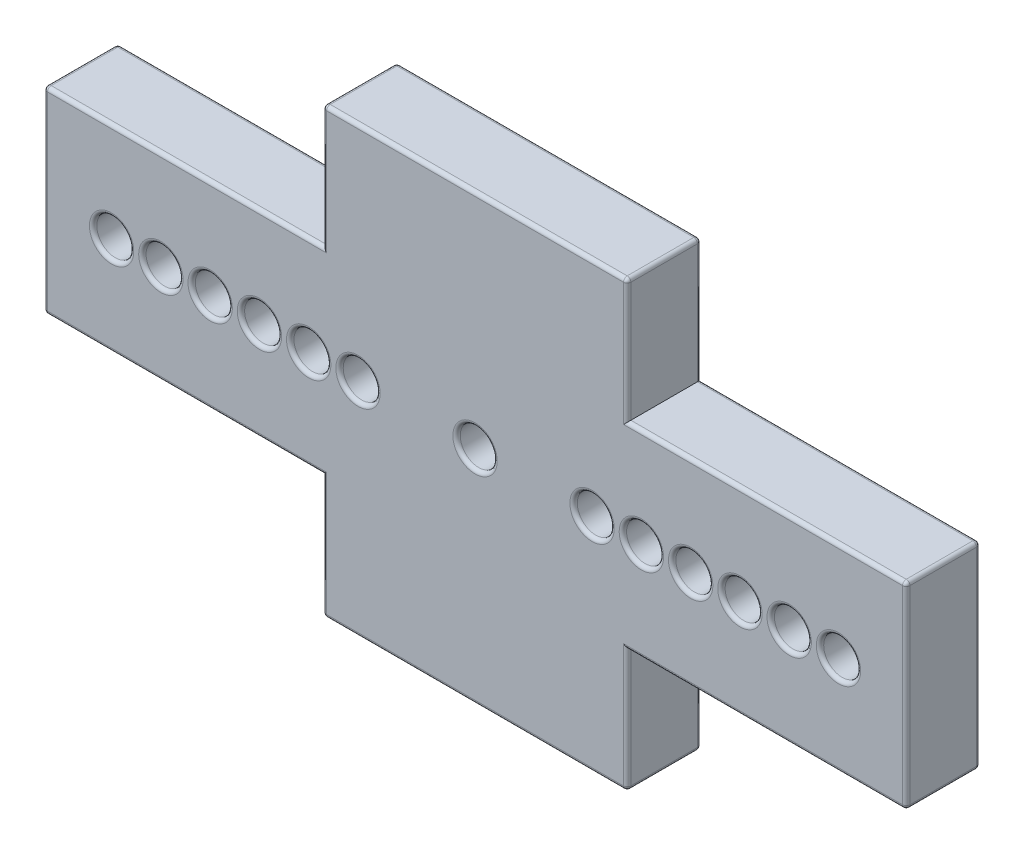
SolidWorks part; units mm, degrees
ref_plane "Ön Düzlem" through (0, 0, 0) normal (0, 0, 1) x (1, 0, 0)
ref_plane "Üst Düzlem" through (0, 0, 0) normal (0, 1, 0) x (1, 0, 0)
ref_plane "Sağ Düzlem" through (0, 0, 0) normal (1, 0, 0) x (0, 0, -1)
sketch "Sketch1" plane through (0, 0, 0) normal (0, 0, 1) x (1, 0, 0)
  line L0 (-17.5, 4) -> (-6.175, 4)
  line L1 (-17.5, -4) -> (17.5, -4) construction
  line L2 (-17.5, -4) -> (-17.5, 4) construction
  line L3 (-17.5, 4) -> (17.5, 4) construction
  line L4 (17.5, -4) -> (17.5, 4) construction
  line L5 (-17.5, -4) -> (17.5, 4) construction
  line L6 (-17.5, 4) -> (17.5, -4) construction
  line L7 (-6.175, -9) -> (6.175, -9) construction
  line L8 (-6.175, -9) -> (-6.175, 9) construction
  line L9 (-6.175, 9) -> (6.175, 9) construction
  line L10 (6.175, -9) -> (6.175, 9) construction
  line L11 (-6.175, -9) -> (6.175, 9) construction
  line L12 (-6.175, 9) -> (6.175, -9) construction
  line L13 (-6.175, 4) -> (-6.175, 9)
  line L14 (-6.175, 9) -> (6.175, 9)
  line L15 (6.175, 9) -> (6.175, 4)
  line L16 (6.175, 4) -> (17.5, 4)
  line L17 (17.5, 4) -> (17.5, -4)
  line L18 (17.5, -4) -> (6.175, -4)
  line L19 (6.175, -4) -> (6.175, -9)
  line L20 (6.175, -9) -> (-6.175, -9)
  line L21 (-6.175, -9) -> (-6.175, -4)
  line L22 (-6.175, -4) -> (-17.5, -4)
  line L23 (-17.5, -4) -> (-17.5, 4)
  circle A0 centre (0, 0) radius 0.75
  point P0 (0, 0)
  point P6 (0, 0)
  dimension "D5" = 1.5
  dimension "D1" = 8
  dimension "D2" = 12.35
  dimension "D3" = 35
  dimension "D4" = 18
extrude "Boss-Extrude1" add sketch "Sketch1" along normal mid plane 3
sketch "Sketch3" plane through (0, 0, 1.5) normal (0, 0, 1) x (1, 0, 0)
  line L0 (-17.5, 4) -> (-17.5, -4) construction
  circle A0 centre (-14.75, 0) radius 0.75
  circle A1 centre (-12.75, 0) radius 0.75
  circle A2 centre (-10.75, 0) radius 0.75
  circle A3 centre (-8.75, 0) radius 0.75
  circle A4 centre (-6.75, 0) radius 0.75
  circle A5 centre (-4.75, 0) radius 0.75
  point P4 (0, 0)
  dimension "D1" = 1.5
  dimension "D2" = 2.75
  dimension "D4" = 2
  dimension "D3" = 6
extrude "Cut-Extrude1" cut sketch "Sketch3" against normal through all
mirror "Mirror1" about plane through (0, 0, 0) normal (1, 0, 0) of "Cut-Extrude1"
fillet "Fillet1" radius 0.15 58 edges at (4, 0, 1.5) (4, 0, -1.5) (6, 0, 1.5) (6, 0, -1.5) (8, 0, 1.5) (8, 0, -1.5) (10, 0, 1.5) (10, 0, -1.5) (12, 0, 1.5) (12, 0, -1.5) (14, 0, 1.5) (14, 0, -1.5) (-4, 0, 1.5) (-4, 0, -1.5) (-6, 0, 1.5) (-6, 0, -1.5) (-8, 0, 1.5) (-8, 0, -1.5) (-10, 0, 1.5) (-10, 0, -1.5) (-12, 0, 1.5) (-12, 0, -1.5) (-14, 0, 1.5) (-14, 0, -1.5) (0.75, 0, -1.5) (0.75, 0, 1.5) (17.5, 0, -1.5) (11.8375, 4, -1.5) (6.175, 6.5, -1.5) (0, 9, -1.5) (-6.175, 6.5, -1.5) (-11.8375, 4, -1.5) (-17.5, 0, -1.5) (-11.8375, -4, -1.5) (-6.175, -6.5, -1.5) (0, -9, -1.5) (6.175, -6.5, -1.5) (11.8375, -4, -1.5) (17.5, 0, 1.5) (11.8375, 4, 1.5) (6.175, 6.5, 1.5) (0, 9, 1.5) (-6.175, 6.5, 1.5) (-11.8375, 4, 1.5) (-17.5, 0, 1.5) (-11.8375, -4, 1.5) (-6.175, -6.5, 1.5) (0, -9, 1.5) (6.175, -6.5, 1.5) (11.8375, -4, 1.5) (17.5, -4, 0) (-6.175, -9, 0) (-17.5, -4, 0) (-17.5, 4, 0) (-6.175, 9, 0) (6.175, 9, 0) (17.5, 4, 0) (6.175, -9, 0)
